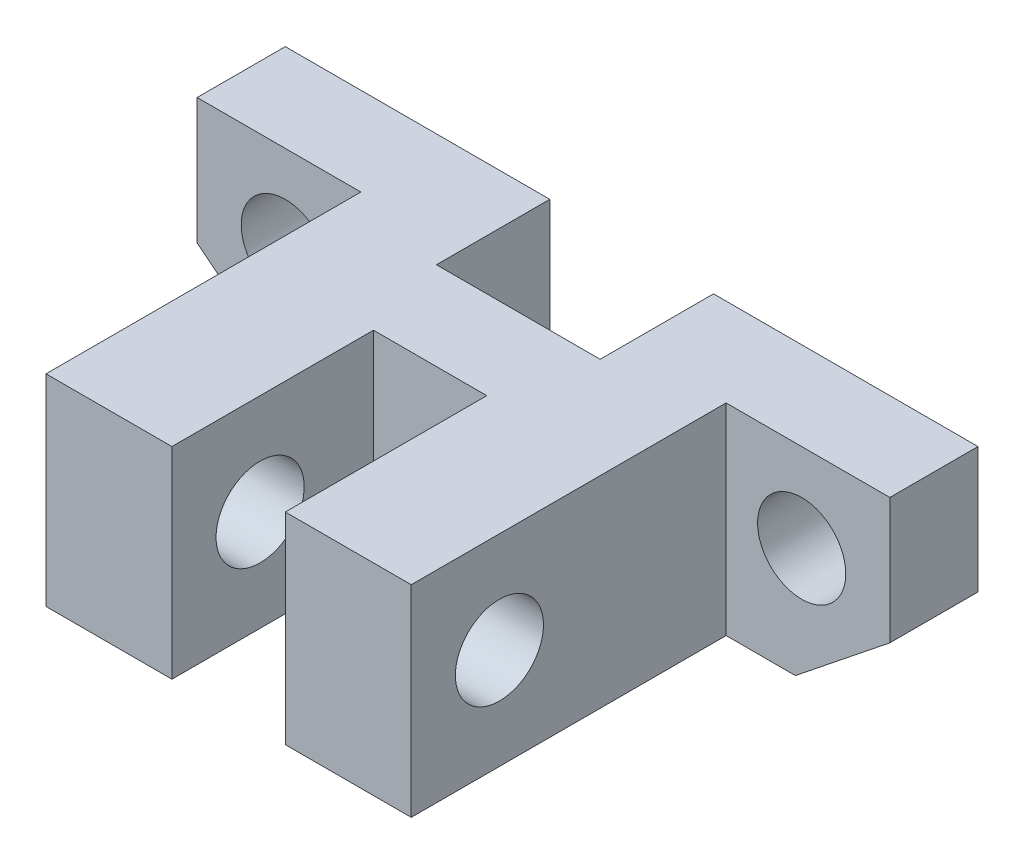
SolidWorks part; units mm, degrees
ref_plane "Alzado" through (0, 0, 0) normal (0, 0, 1) x (1, 0, 0)
ref_plane "Planta" through (0, 0, 0) normal (0, 1, 0) x (1, 0, 0)
ref_plane "Vista lateral" through (0, 0, 0) normal (1, 0, 0) x (0, 0, -1)
sketch "Croquis1" plane through (0, 0, 0) normal (0, 0, 1) x (1, 0, 0)
  line L0 (-20, -11) -> (-27.5, -5)
  line L1 (-27.5, 5) -> (27.5, 5)
  line L2 (-27.5, 5) -> (-27.5, -5)
  line L4 (27.5, 5) -> (27.5, -5)
  line L7 (-20, -11) -> (20, -11)
  line L13 (20, -11) -> (27.5, -5)
  point P0 (0, 0)
  point P5 (0, -8)
  dimension "D1" = 55
  dimension "D2" = 10
  dimension "D4" = 40
  dimension "D5" = 16
extrude "Saliente-Extruir1" add sketch "Croquis1" along normal blind 32
sketch "Croquis3" plane through (27.5, 0, 0) normal (1, 0, 0) x (0, 0, -1)
  line L0 (0, -5) -> (0, 5) construction
  line L1 (-35.1492, 16.7278) -> (-7, 16.7278)
  line L2 (-35.1492, 16.7278) -> (-35.1492, -16.7278)
  line L3 (-35.1492, -16.7278) -> (-7, -16.7278)
  line L4 (-7, 16.7278) -> (-7, -16.7278)
  line L5 (-35.1492, 16.7278) -> (-7, -16.7278) construction
  line L6 (-35.1492, -16.7278) -> (-7, 16.7278) construction
  point P0 (-21.0746, 0)
  dimension "D1" = 7
extrude "Cortar-Extruir1" cut sketch "Croquis3" against normal blind 13
sketch "Croquis4" plane through (-27.5, 0, 0) normal (-1, 0, 0) x (0, 0, 1)
  line L0 (0, 5) -> (0, -5) construction
  line L1 (7, 10.792) -> (39.2728, 10.792)
  line L2 (7, 10.792) -> (7, -18.4858)
  line L3 (7, -18.4858) -> (39.2728, -18.4858)
  line L4 (39.2728, 10.792) -> (39.2728, -18.4858)
  line L5 (7, 10.792) -> (39.2728, -18.4858) construction
  line L6 (7, -18.4858) -> (39.2728, 10.792) construction
  point P0 (23.1364, -3.8469)
  dimension "D1" = 7
extrude "Cortar-Extruir2" cut sketch "Croquis4" against normal blind 13
sketch "Croquis5" plane through (0, -11, 0) normal (0, -1, 0) x (1, 0, 0)
  line L0 (-20, 0) -> (20, 0) construction
  line L1 (-6.5, 9) -> (6.5, 9)
  line L2 (-6.5, 9) -> (-6.5, 0)
  line L3 (-6.5, 0) -> (6.5, 0)
  line L4 (6.5, 9) -> (6.5, 0)
  line L5 (-6.5, 9) -> (6.5, 0) construction
  line L6 (-6.5, 0) -> (6.5, 9) construction
  point P0 (0, 4.5)
  dimension "D1" = 13
  dimension "D2" = 6.5
  dimension "D3" = 9
extrude "Cortar-Extruir3" cut sketch "Croquis5" against normal through all
sketch "Croquis6" plane through (0, -11, 0) normal (0, -1, 0) x (1, 0, 0)
  line L0 (6.5, 9) -> (-6.5, 9) construction
  line L1 (-4.5, 16) -> (4.5, 16)
  line L2 (-4.5, 16) -> (-4.5, 39)
  line L3 (-4.5, 39) -> (4.5, 39)
  line L4 (4.5, 16) -> (4.5, 39)
  line L5 (-4.5, 16) -> (4.5, 39) construction
  line L6 (-4.5, 39) -> (4.5, 16) construction
  point P0 (0, 27.5)
  dimension "D1" = 9
  dimension "D2" = 4.5
  dimension "D4" = 7
extrude "Cortar-Extruir4" cut sketch "Croquis6" against normal through all
sketch "Croquis7" plane through (14.5, 0, 0) normal (1, 0, 0) x (0, 0, -1)
  line L0 (-7, -3) -> (-25, -3) construction
  line L1 (-7, -11) -> (-7, 5) construction
  line L2 (-7, 5) -> (-7, -11) construction
  circle A0 centre (-25, -3) radius 3.5
  point P11 (-7, -3)
  dimension "D1" = 7
  dimension "D2" = 18
extrude "Cortar-Extruir5" cut sketch "Croquis7" against normal through all
sketch "Croquis9" plane through (0, 0, 7) normal (0, 0, 1) x (1, 0, 0)
  line L0 (-27.5, 5) -> (-14.5, 5) construction
  line L1 (14.5, 5) -> (27.5, 5) construction
  line L3 (-27.5, 5) -> (-27.5, -5) construction
  line L4 (27.5, -5) -> (27.5, 5) construction
  circle A0 centre (20.5, -2) radius 3.5
  circle A1 centre (-20.5, -2) radius 3.5
  dimension "D1" = 7
  dimension "D2" = 7
  dimension "D3" = 7
  dimension "D4" = 7
  dimension "D5" = 7
  dimension "D6" = 7
extrude "Cortar-Extruir6" cut sketch "Croquis9" against normal through all
